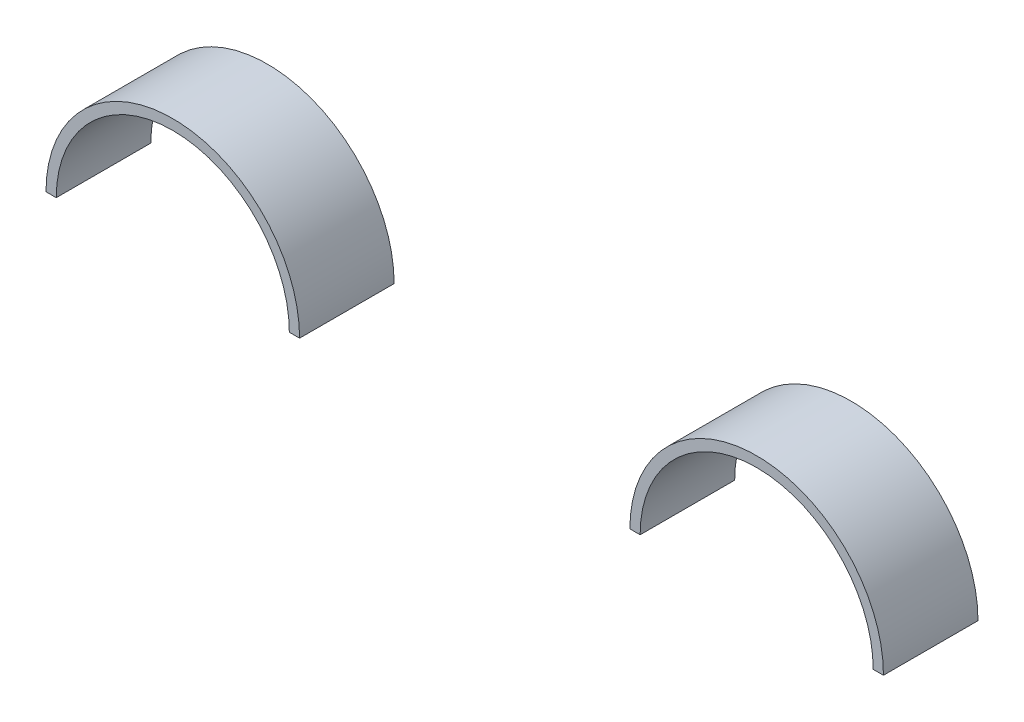
SolidWorks part; units mm, degrees
material "Velcro"
ref_plane "Front Plane" through (0, 0, 0) normal (0, 0, 1) x (1, 0, 0)
ref_plane "Top Plane" through (0, 0, 0) normal (0, 1, 0) x (1, 0, 0)
ref_plane "Right Plane" through (0, 0, 0) normal (1, 0, 0) x (0, 0, -1)
sketch "Sketch1" plane through (0, 0, 563.2423) normal (0, 0, -1) x (0, -1, 0)
  line L0 (326.7906, -1399.2805) -> (326.7906, -1499.2805) construction
  line L1 (326.7906, -1399.2805) -> (326.7906, -1499.2805) construction
  line L2 (326.7906, -1649.7805) -> (326.7906, -1749.7805) construction
  line L3 (326.7906, -1649.7805) -> (326.7906, -1749.7805) construction
  line L4 (326.7906, -1394.8805) -> (326.7906, -1399.2805)
  line L5 (326.7906, -1503.6805) -> (326.7906, -1499.2805)
  line L6 (326.7906, -1749.7805) -> (326.7906, -1754.1805)
  line L7 (326.7906, -1645.3805) -> (326.7906, -1649.7805)
  arc A0 (326.7906, -1749.7805) -> (326.7906, -1649.7805) centre (326.7906, -1699.7805) cw
  arc A1 (326.7906, -1499.2805) -> (326.7906, -1399.2805) centre (326.7906, -1449.2805) cw
  arc A2 (326.7906, -1503.6805) -> (326.7906, -1394.8805) centre (326.7906, -1449.2805) cw
  arc A3 (326.7906, -1754.1805) -> (326.7906, -1645.3805) centre (326.7906, -1699.7805) cw
  dimension "D1" = 4.4
  dimension "D2" = 4.4
extrude "Boss-Extrude1" add sketch "Sketch1" along normal blind 40.56
